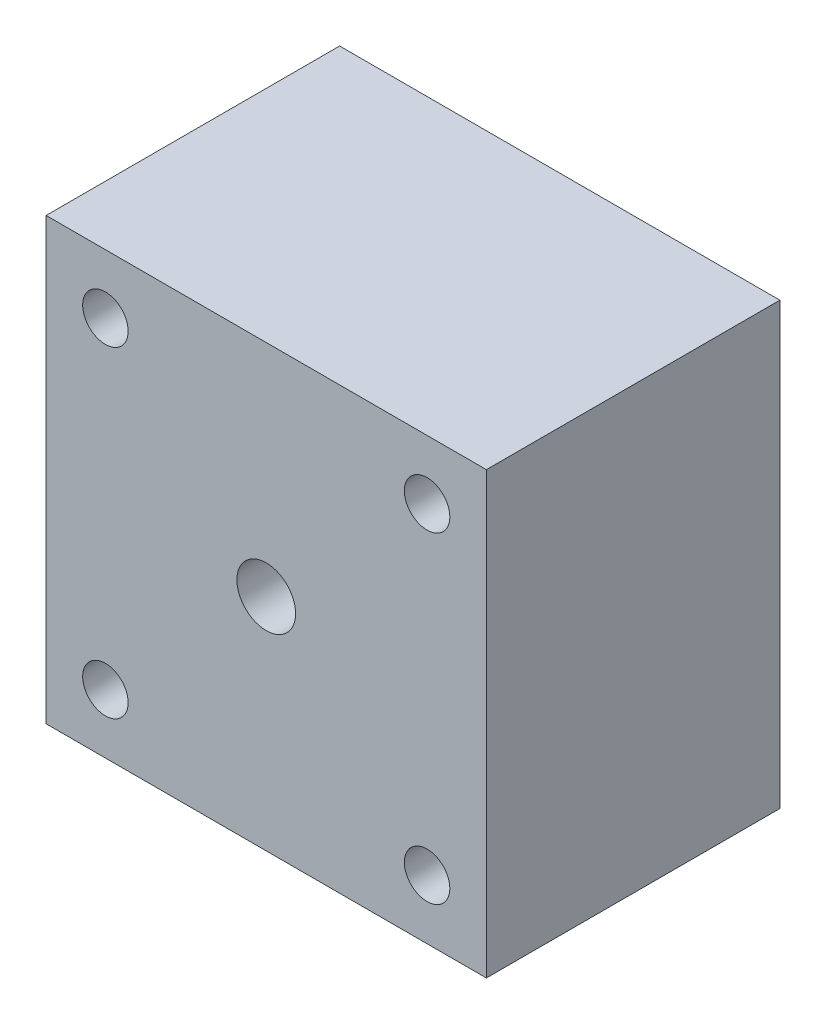
SolidWorks part; units mm, degrees
other "Markup1"
sketch "Sketch2" plane through (-15, -15, 20) normal (-0.8626, -0.0457, 0.5038) x (0.0966, -0.9925, 0.0754)
ref_plane "Front Plane" through (0, 0, 0) normal (0, 0, 1) x (1, 0, 0)
ref_plane "Top Plane" through (0, 0, 0) normal (0, 1, 0) x (1, 0, 0)
ref_plane "Right Plane" through (0, 0, 0) normal (1, 0, 0) x (0, 0, -1)
sketch "Sketch1" plane through (0, 0, 0) normal (0, 0, 1) x (1, 0, 0)
  line L0 (0, 10.9602) -> (0, -10.9602)
  line L1 (15, -15) -> (-15, -15)
  line L2 (15, -15) -> (15, 15)
  line L3 (15, 15) -> (-15, 15)
  line L4 (-15, -15) -> (-15, 15)
  line L5 (15, -15) -> (-15, 15) construction
  line L6 (15, 15) -> (-15, -15) construction
  line L7 (10.9602, -10.9602) -> (-10.9602, -10.9602)
  line L8 (10.9602, -10.9602) -> (10.9602, 10.9602)
  line L9 (10.9602, 10.9602) -> (-10.9602, 10.9602)
  line L10 (-10.9602, -10.9602) -> (-10.9602, 10.9602)
  line L11 (10.9602, -10.9602) -> (-10.9602, 10.9602) construction
  line L12 (10.9602, 10.9602) -> (-10.9602, -10.9602) construction
  line L13 (-10.9602, 0) -> (10.9602, 0)
  circle A0 centre (-10.9602, 10.9602) radius 1.55
  circle A1 centre (10.9602, 10.9602) radius 1.55
  circle A2 centre (10.9602, -10.9602) radius 1.55
  circle A3 centre (-10.9602, -10.9602) radius 1.55
  point P0 (0, 0)
  point P6 (0, 0)
  dimension "D2" = 3.1
  dimension "D1" = 31
  dimension "D3" = 30
extrude "Boss-Extrude1" add sketch "Sketch1" along normal blind 20 contours L4 L1 L2 L3 L7 A3 L10 A0 L9 A1 L8 A2 | A0 L10 L13 L0 L9 | L8 A1 L9 L0 L13 | L10 A3 L7 L0 L13 | A2 L8 L13 L0 L7
sketch "Sketch3" plane through (0, 0, 20) normal (0, 0, 1) x (1, 0, 0)
  circle A0 centre (0, 0) radius 2
  dimension "D1" = 4
extrude "Cut-Extrude1" cut sketch "Sketch3" against normal blind 10
equation "\"a\"=30"
equation "\"D3@Sketch1\"=\"a\""
equation "\"b\"=20"
equation "\"D1@Boss-Extrude1\"=\"b\""
